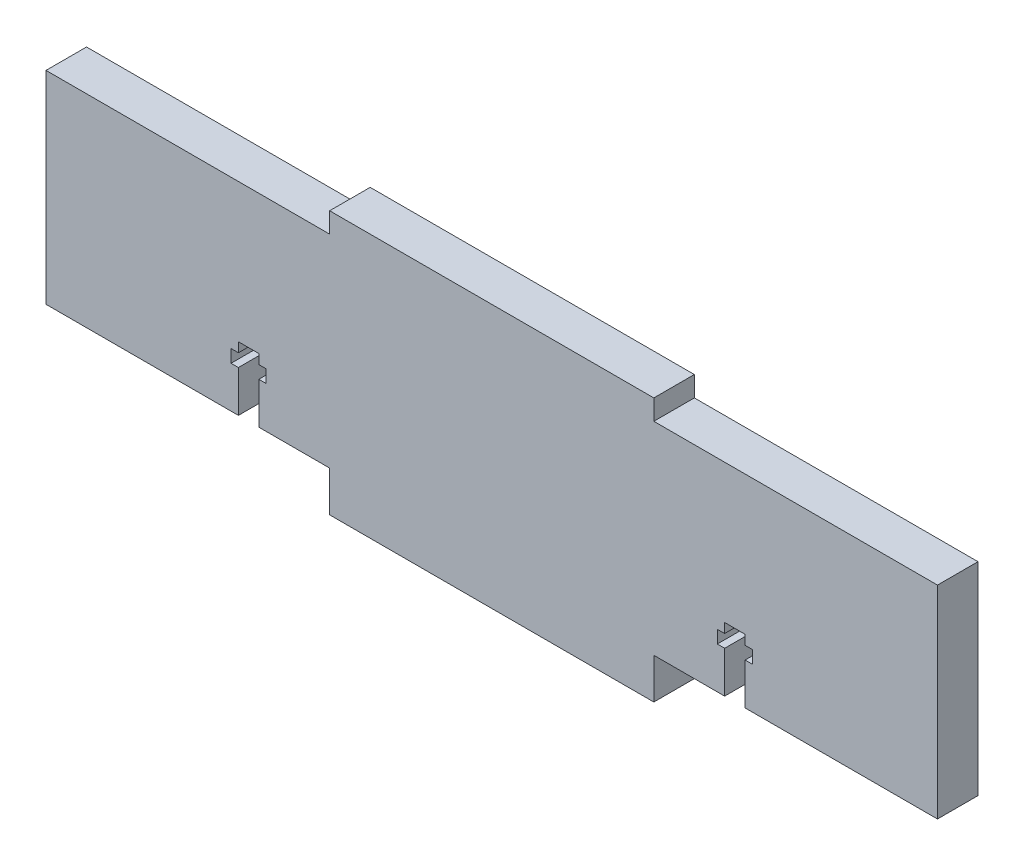
SolidWorks part; units mm, degrees
ref_plane "Front Plane" through (0, 0, 0) normal (0, 0, 1) x (1, 0, 0)
ref_plane "Top Plane" through (0, 0, 0) normal (0, 1, 0) x (1, 0, 0)
ref_plane "Right Plane" through (0, 0, 0) normal (1, 0, 0) x (0, 0, -1)
sketch "Sketch1" plane through (0, 0, 0) normal (0, 0, 1) x (1, 0, 0)
  line L0 (44.45, -3.175) -> (0, -3.175) construction
  line L1 (0, 0) -> (44.45, 0)
  line L2 (0, 0) -> (0, 31.75)
  line L3 (0, 31.75) -> (44.45, 31.75)
  line L4 (139.7, 0) -> (139.7, 31.75)
  line L5 (95.25, 31.75) -> (139.7, 31.75)
  line L6 (44.45, 0) -> (44.45, -6.35)
  line L7 (44.45, -6.35) -> (95.25, -6.35)
  line L8 (95.25, 0) -> (95.25, -6.35)
  line L9 (95.25, -3.175) -> (139.7, -3.175) construction
  line L10 (95.25, 0) -> (139.7, 0)
  line L12 (44.45, 31.75) -> (44.45, 34.925)
  line L13 (44.45, 34.925) -> (95.25, 34.925)
  line L14 (95.25, 31.75) -> (95.25, 34.925)
  dimension "D1" = 139.7
  dimension "D2" = 31.75
  dimension "D3" = 50.8
  dimension "D4" = 6.35
  dimension "D5" = 3.175
  dimension "D6" = 50.8
extrude "Boss-Extrude1" add sketch "Sketch1" along normal blind 6.35
sketch "Sketch2" plane through (0, 0, 6.35) normal (0, 0, 1) x (1, 0, 0)
  line L0 (0, 0) -> (44.45, 0) construction
  line L1 (30.15, 0) -> (33.35, 0)
  line L2 (30.15, 0) -> (30.15, 6.5)
  line L3 (30.15, 10) -> (33.35, 10)
  line L4 (33.35, 0) -> (33.35, 6.5)
  line L5 (69.85, -6.35) -> (69.85, 34.925) construction
  line L6 (44.45, -6.35) -> (95.25, -6.35) construction
  line L8 (44.45, -3.175) -> (31.75, -3.175) construction
  line L9 (44.45, 0) -> (44.45, -6.35) construction
  line L10 (31.75, -3.175) -> (31.75, 0) construction
  line L11 (29, 7.5) -> (34.5, 7.5) construction
  line L12 (30.15, 8.5) -> (29, 8.5)
  line L13 (33.35, 8.5) -> (33.35, 10)
  line L14 (30.15, 6.5) -> (29, 6.5)
  line L15 (29, 8.5) -> (29, 6.5)
  line L16 (33.35, 8.5) -> (34.5, 8.5)
  line L17 (110.7, 7.5) -> (105.2, 7.5) construction
  line L18 (33.35, 6.5) -> (34.5, 6.5)
  line L19 (34.5, 8.5) -> (34.5, 6.5)
  line L20 (30.15, 8.5) -> (30.15, 10)
  line L21 (109.55, 8.5) -> (109.55, 10)
  line L22 (105.2, 8.5) -> (105.2, 6.5)
  line L23 (106.35, 6.5) -> (105.2, 6.5)
  line L24 (106.35, 8.5) -> (105.2, 8.5)
  line L25 (110.7, 8.5) -> (110.7, 6.5)
  line L26 (109.55, 6.5) -> (110.7, 6.5)
  line L27 (106.35, 8.5) -> (106.35, 10)
  line L28 (109.55, 8.5) -> (110.7, 8.5)
  line L29 (106.35, 0) -> (106.35, 6.5)
  line L30 (109.55, 10) -> (106.35, 10)
  line L31 (109.55, 0) -> (109.55, 6.5)
  line L32 (109.55, 0) -> (106.35, 0)
  line L34 (95.25, 34.925) -> (44.45, 34.925) construction
  dimension "D1" = 10
  dimension "D2" = 3.2
  dimension "D3" = 7.5
  dimension "D4" = 5.5
  dimension "D5" = 12.7
  dimension "D6" = 2
extrude "Cut-Extrude1" cut sketch "Sketch2" against normal through all
